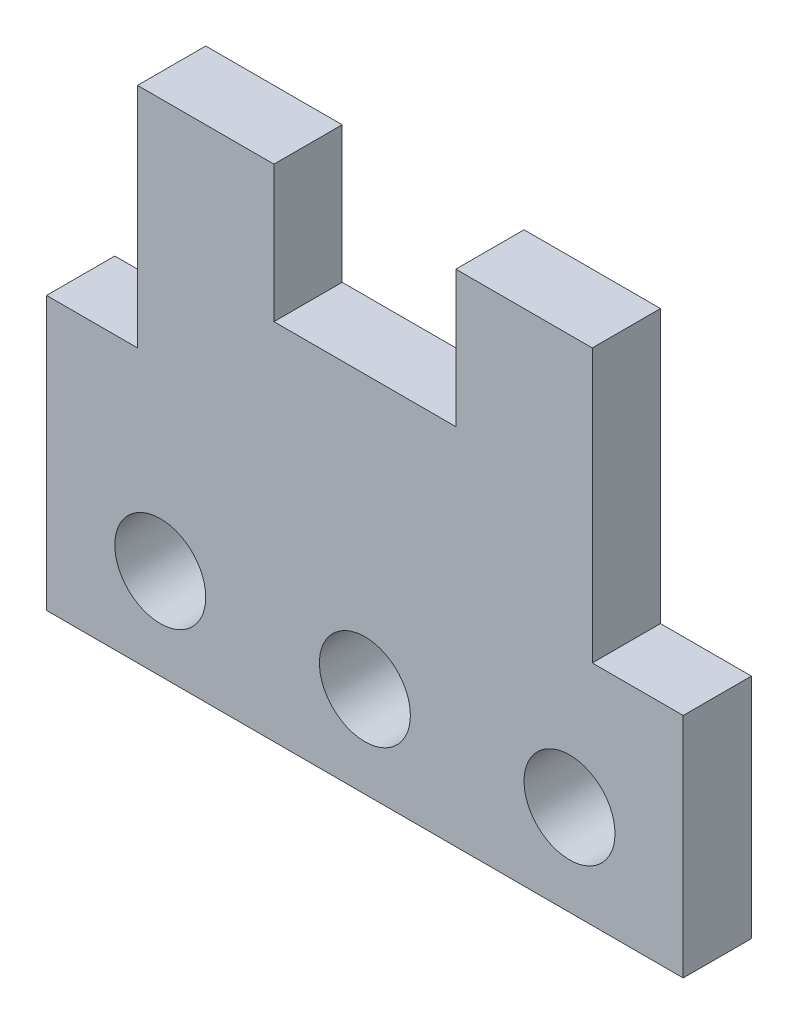
SolidWorks part; units mm, degrees
ref_plane "Front Plane" through (0, 0, 0) normal (0, 0, 1) x (1, 0, 0)
ref_plane "Top Plane" through (0, 0, 0) normal (0, 1, 0) x (1, 0, 0)
ref_plane "Right Plane" through (0, 0, 0) normal (1, 0, 0) x (0, 0, -1)
sketch "Sketch1"
  line L0 (-70, 19.8089) -> (-70, -40.1911)
  line L1 (-70, -40.1911) -> (70, -40.1911)
  line L2 (70, -40.1911) -> (70, 9.8089)
  line L3 (70, 9.8089) -> (50, 9.8089)
  line L4 (50, 9.8089) -> (50, 69.8089)
  line L5 (50, 69.8089) -> (20, 69.8089)
  line L6 (20, 69.8089) -> (20, 39.8089)
  line L7 (20, 39.8089) -> (-20, 39.8089)
  line L8 (-20, 39.8089) -> (-20, 69.8089)
  line L9 (-20, 69.8089) -> (-50, 69.8089)
  line L10 (-50, 69.8089) -> (-50, 19.8089)
  line L11 (-50, 19.8089) -> (-70, 19.8089)
  circle A0 centre (-45, -20.1911) radius 10
  circle A1 centre (0, -20.1911) radius 10
  circle A2 centre (45, -20.1911) radius 10
  point P0 (0, -40.1911)
  point P16 (-134.4785, 23.3492)
  point P21 (0, 0)
  point P22 (0, 0)
  point P23 (0, 0)
  point P24 (-159.2659, 74.9101)
other "AlignGroup1" parameters "D1"=5.3004, "D2"=22.0481, "D6"=20, "D7"=20, "D10"=20, "D17"=20, "D3"=51.0528, "D4"=60, "D5"=89.78, "D8"=57.0737, "D9"=162.0576, "D11"=62.7622, "D12"=27.1657, "D13"=50, "D14"=20, "D15"=0, "D16"=0
other "AlignGroup2"
extrude "Boss-Extrude1" add sketch "Sketch1" along normal blind 15
